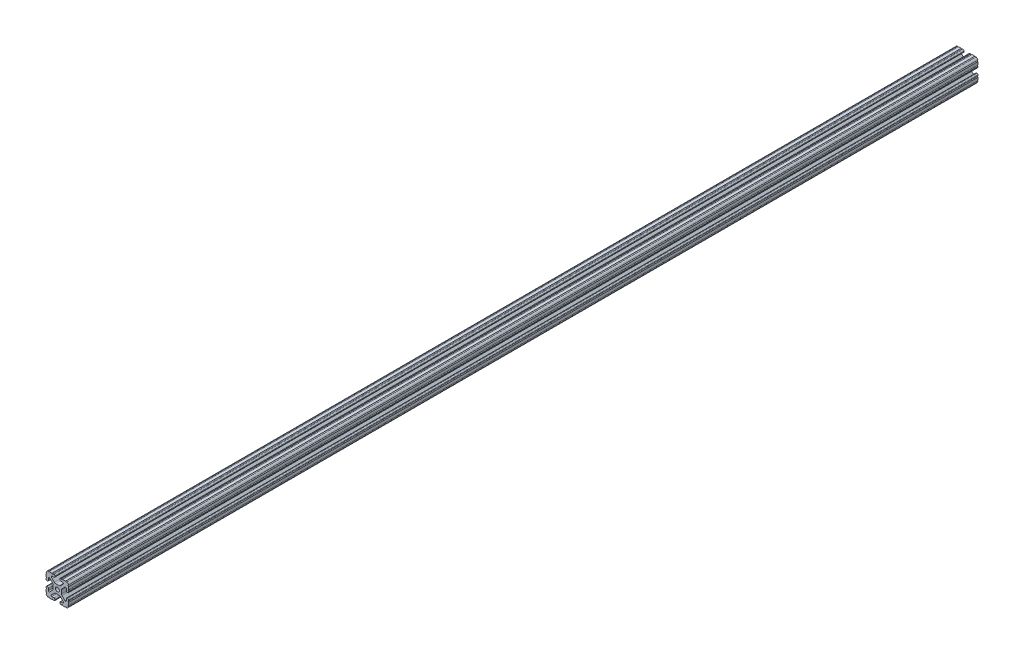
SolidWorks part; units mm, degrees
ref_plane "Front Plane" through (0, 0, 0) normal (0, 0, 1) x (1, 0, 0)
ref_plane "Top Plane" through (0, 0, 0) normal (0, 1, 0) x (1, 0, 0)
ref_plane "Right Plane" through (0, 0, 0) normal (1, 0, 0) x (0, 0, -1)
sketch "Sketch2" plane through (0, 0, 0) normal (0, 0, 1) x (1, 0, 0)
  line L0 (0, 19.05) -> (0, -19.05) construction
  line L1 (-19.05, 0) -> (19.05, 0) construction
  line L2 (4.064, -19.05) -> (19.05, -19.05)
  line L3 (19.05, -19.05) -> (19.05, -4.064)
  line L4 (4.064, -19.05) -> (4.064, -14.986)
  line L5 (4.064, -14.986) -> (12.1123, -14.986)
  line L6 (12.1123, -14.986) -> (4.1113, -6.985)
  line L7 (0, 0) -> (19.05, -19.05) construction
  line L8 (19.05, -4.064) -> (14.986, -4.064)
  line L9 (14.986, -4.064) -> (14.986, -12.1123)
  line L10 (14.986, -12.1123) -> (6.985, -4.1113)
  circle A0 centre (0, 0) radius 3.3274
  arc A1 (8.9963, -14.986) -> (9.909, -12.7826) centre (8.9963, -13.6953) ccw construction
  point P8 (0, -6.985)
  dimension "Center Hole Diameter" = 6.6548
  dimension "Rail Height" = 38.1
  dimension "Rail Width" = 38.1
  dimension "T-Slot Width" = 8.128
  dimension "Slot Inner Width" = 20.574
  dimension "Thickness" = 4.064
  dimension "Slot Depth" = 8.001
  dimension "D1" = 4.064
sketch "Sketch3" plane through (0, 0, 0) normal (1, 0, 0) x (0, 0, -1)
  line L0 (-762, -19.05) -> (762, -19.05) construction
  line L1 (-736.6, 0) -> (736.6, 0) construction
  dimension "Length" = 1524
  dimension "D1" = 25.4
sketch "Sketch4" plane through (0, 0, 0) normal (0, 0, 1) x (1, 0, 0)
  line L0 (5.7912, -19.05) -> (14.3002, -19.05)
  line L1 (4.064, -19.05) -> (19.05, -19.05) construction
  line L2 (4.064, -19.05) -> (4.064, -14.986) construction
  line L3 (4.064, -14.986) -> (12.1123, -14.986) construction
  line L4 (4.064, -16.7132) -> (4.064, -17.3228)
  line L5 (5.7912, -14.986) -> (8.9963, -14.986)
  line L6 (0, -6.985) -> (2.833, -6.985)
  line L7 (12.1123, -14.986) -> (4.1113, -6.985) construction
  line L8 (5.0152, -7.8889) -> (9.909, -12.7826)
  line L9 (19.05, -19.05) -> (19.05, -4.064) construction
  line L10 (14.986, -12.1123) -> (6.985, -4.1113) construction
  line L11 (14.986, -4.064) -> (14.986, -12.1123) construction
  line L12 (14.986, -8.9963) -> (14.986, -5.7912)
  line L13 (19.05, -4.064) -> (14.986, -4.064) construction
  line L14 (16.7132, -4.064) -> (17.3228, -4.064)
  line L15 (19.05, -5.7912) -> (19.05, -14.3002)
  line L16 (12.7826, -9.909) -> (7.8889, -5.0152)
  line L17 (6.985, 0) -> (6.985, -2.833)
  line L18 (-19.05, 0) -> (19.05, 0) construction
  line L19 (0, -6.985) -> (0, -3.3274)
  line L20 (0, 19.05) -> (0, -19.05) construction
  line L21 (6.985, 0) -> (3.3274, 0)
  arc A0 (4.064, -17.3228) -> (5.7912, -19.05) centre (5.7912, -17.3228) ccw
  arc A2 (4.064, -16.7132) -> (5.7912, -14.986) centre (5.7912, -16.7132) cw
  arc A3 (8.9963, -14.986) -> (9.909, -12.7826) centre (8.9963, -13.6953) ccw
  arc A4 (2.833, -6.985) -> (5.0152, -7.8889) centre (2.833, -10.0711) cw
  arc A5 (14.3002, -19.05) -> (19.05, -14.3002) centre (14.3002, -14.3002) ccw
  arc A6 (12.7826, -9.909) -> (14.986, -8.9963) centre (13.6953, -8.9963) ccw
  arc A7 (14.986, -5.7912) -> (16.7132, -4.064) centre (16.7132, -5.7912) cw
  arc A8 (17.3228, -4.064) -> (19.05, -5.7912) centre (17.3228, -5.7912) cw
  arc A9 (7.8889, -5.0152) -> (6.985, -2.833) centre (10.0711, -2.833) cw
  circle A10 centre (0, 0) radius 3.3274 construction
  arc A11 (0, -3.3274) -> (3.3274, 0) centre (0, 0) ccw
  dimension "D1" = 4.7498
  dimension "D2" = 3.0861
  dimension "D3" = 1.7272
extrude "Boss-Extrude1" add sketch "Sketch4" along normal mid plane 1524
sketch "Sketch5" plane through (0, 0, 0) normal (0, 0, 1) x (1, 0, 0)
  line L0 (4.064, -19.05) -> (19.05, -19.05) construction
  line L1 (5.7912, -14.986) -> (8.9963, -14.986) construction
  line L3 (0, 0) -> (19.05, -19.05) construction
  line L4 (8.9963, -14.986) -> (8.9963, -19.05) construction
  line L5 (12.1123, -14.986) -> (4.1113, -6.985) construction
  circle A0 centre (14.7395, -19.05) radius 1.016
  circle A1 centre (7.9803, -19.05) radius 1.016
  circle A2 centre (19.05, -14.7395) radius 1.016
  circle A3 centre (19.05, -7.9803) radius 1.016
  point P10 (7.3938, -14.986)
  point P12 (13.6953, -8.9963)
  dimension "D1" = 2.032
extrude "Cut-Extrude1" cut sketch "Sketch5" against normal through all both and the other way through all
mirror "Mirror1" about plane through (0, 0, 0) normal (1, 0, 0) of bodies 137 134
mirror "Mirror2" about plane through (0, 0, 0) normal (0, 1, 0) of bodies 135
equation "\"D1@Boss-Extrude1\"=\"Length@Sketch3\""
equation "\"D1@Sketch2\"=\"Thickness@Sketch2\""
equation "\"D2@Sketch4\"=\"Slot Inner Width@Sketch2\"*0.15"
equation "\"D1@Sketch4\"=\"D3@Sketch4\"*2.75"
equation "\"D3@Sketch4\"=\"Thickness@Sketch2\"*0.425"
equation "\"D1@Sketch5\"=\"Thickness@Sketch2\"*0.5"
